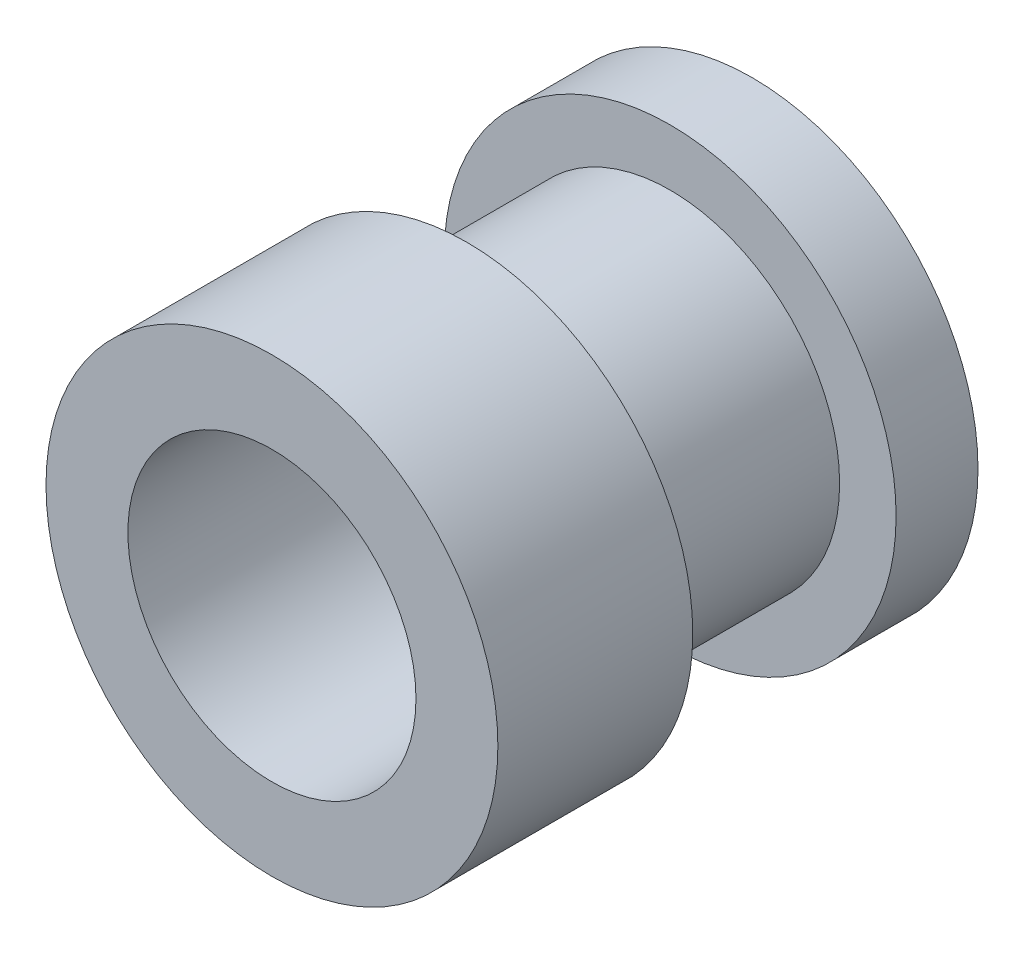
SolidWorks part; units mm, degrees
ref_plane "Front Plane" through (0, 0, 0) normal (0, 0, 1) x (1, 0, 0)
ref_plane "Top Plane" through (0, 0, 0) normal (0, 1, 0) x (1, 0, 0)
ref_plane "Right Plane" through (0, 0, 0) normal (1, 0, 0) x (0, 0, -1)
sketch "Sketch1" plane through (0, 0, 0) normal (0, 0, 1) x (1, 0, 0)
  circle A0 centre (0, 0) radius 3.81
  circle A1 centre (0, 0) radius 3.2385
  dimension "D1" = 7.62
  dimension "D2" = 6.477
extrude "Boss-Extrude1" add sketch "Sketch1" along normal blind 10.795
ref_plane "Plane1" through (0, 0, 5.3975) normal (0, 0, 1) x (1, 0, 0)
ref_plane "Plane2" through (0, 0, 6.4135) normal (0, 0, 1) x (1, 0, 0)
ref_plane "Plane4" through (0, 0, 1.8415) normal (0, 0, 1) x (1, 0, 0)
sketch "Sketch3" plane through (0, 0, 1.8415) normal (0, 0, 1) x (1, 0, 0)
  circle A0 centre (0, 0) radius 5.08
  circle A1 centre (0, 0) radius 3.81
  dimension "D1" = 10.16
extrude "Boss-Extrude2" add sketch "Sketch3" against normal up to surface (1.8415 mm away) up to face at (3.81, 0, 0)
sketch "Sketch4" plane through (0, 0, 6.4135) normal (0, 0, 1) x (1, 0, 0)
  circle A0 centre (0, 0) radius 3.81
  circle A1 centre (0, 0) radius 5.08
  dimension "D1" = 10.16
extrude "Boss-Extrude3" add sketch "Sketch4" along normal up to surface (4.3815 mm away) up to face at (3.81, 0, 10.795)
